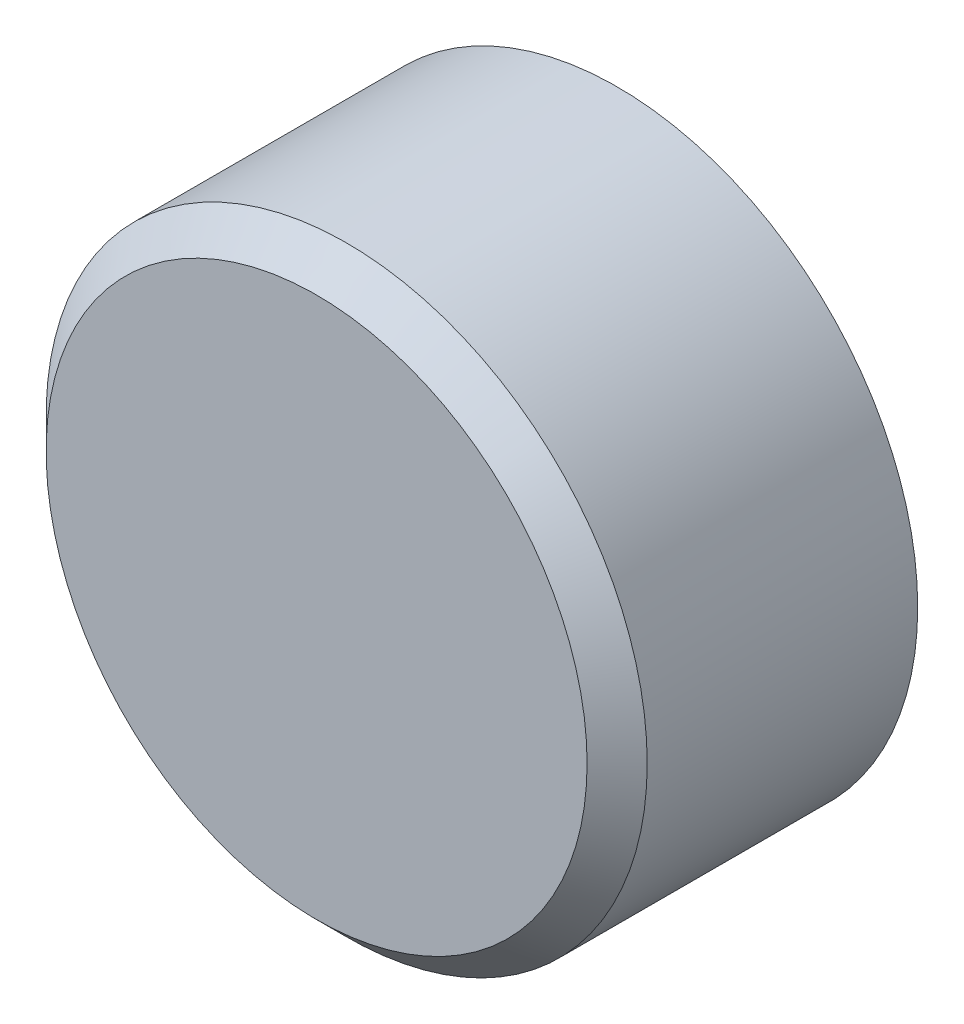
SolidWorks part; units mm, degrees
ref_plane "Plan de face" through (0, 0, 0) normal (0, 0, 1) x (1, 0, 0)
ref_plane "Plan de dessus" through (0, 0, 0) normal (0, 1, 0) x (1, 0, 0)
ref_plane "Plan de droite" through (0, 0, 0) normal (1, 0, 0) x (0, 0, -1)
sketch "Esquisse1" plane through (0, 0, 0) normal (0, 0, 1) x (1, 0, 0)
  circle A0 centre (0, 0) radius 20
  dimension "D1" = 40
extrude "Boss.-Extru.1" add sketch "Esquisse1" along normal blind 20
chamfer "Chanfrein1" distance 2 angle 45 1 edges at (20, 0, 20)
